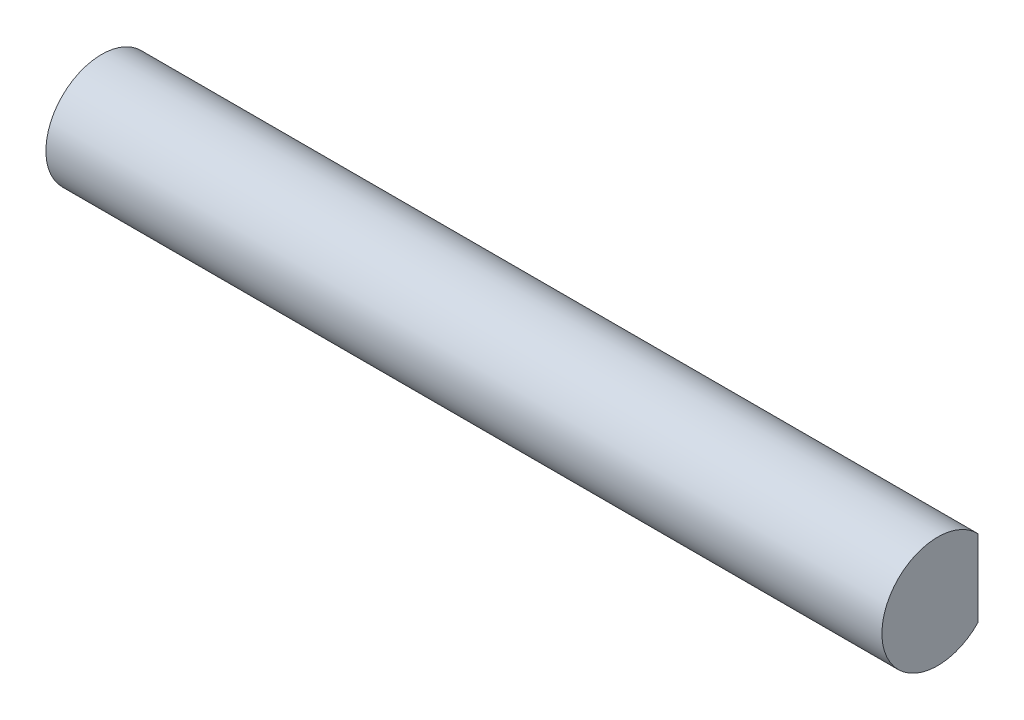
SolidWorks part; units mm, degrees
ref_plane "Front Plane" through (0, 0, 0) normal (0, 0, 1) x (1, 0, 0)
ref_plane "Top Plane" through (0, 0, 0) normal (0, 1, 0) x (1, 0, 0)
ref_plane "Right Plane" through (0, 0, 0) normal (1, 0, 0) x (0, 0, -1)
sketch "Sketch5" plane through (0, 0, 3.7) normal (1, 0, 0) x (0, 1, 0)
  line L0 (0, -16.5814) -> (0, 9.1814) construction
  line L5 (-7.5, -2.6947) -> (-6.4, -4.6) construction
  line L6 (7.5, -2.6947) -> (6.4, -4.6) construction
  line L7 (5.3668, 1) -> (7.5, -2.6947) construction
  line L8 (-5.3668, 1) -> (5.3668, 1) construction
  line L9 (-5.3668, 1) -> (-7.5, -2.6947) construction
  line L10 (7.7309, -2.6947) -> (6.5732, -4.7)
  line L11 (5.4823, 1.2) -> (7.7309, -2.6947)
  line L12 (-5.4823, 1.2) -> (5.4823, 1.2)
  line L13 (-5.4823, 1.2) -> (-7.7309, -2.6947)
  line L14 (-7.7309, -2.6947) -> (-6.5732, -4.7)
  line L15 (-6.5732, -4.7) -> (6.5732, -4.7)
  line L17 (0, -9.7207) -> (0, 9.7207) construction
  line L18 (-6.9, -10.9381) -> (6.9, -10.9381)
  line L19 (0, -10.9381) -> (0, -3.7) construction
  circle A0 centre (0, -3.7) radius 10 construction
  arc A1 (-6.9, -10.9381) -> (6.9, -10.9381) centre (0, -3.7) cw
  point P18 (0, -13.7)
sketch "Sketch8" plane through (0, 0, 3.7) normal (0, -1, 0) x (1, 0, 0)
  line L2 (0, -9.7207) -> (-145, -9.7207)
  line L3 (0, -9.9381) -> (-145, -9.9381)
  line L4 (0, -10.9381) -> (-150, -10.9381)
  point P0 (0, -9.7207)
  point P3 (0, -10.9381)
sketch "Sketch9" plane through (0, 0, 3.7) normal (1, 0, 0) x (0, 1, 0)
  line L0 (-6.9, -10.9381) -> (6.9, -10.9381) construction
  line L3 (-6.9, -10.9381) -> (6.9, -10.9381) construction
  line L4 (-6.4874, -9.9381) -> (6.4874, -9.9381)
  line L5 (-6.4017, -9.7381) -> (6.4017, -9.7381)
  arc A3 (6.9, -10.9381) -> (-6.9, -10.9381) centre (0, -3.7) ccw construction
  arc A4 (6.4874, -9.9381) -> (-6.4874, -9.9381) centre (0, -3.7) ccw
  arc A5 (6.4017, -9.7381) -> (-6.4017, -9.7381) centre (0, -3.7) ccw
sketch "Sketch1" plane through (0, 0, 0) normal (1, 0, 0) x (0, 0, -1)
  line L37 (7.2381, -6.9) -> (7.2381, 6.9) construction
  line L39 (7.2381, -6.9) -> (7.2381, 6.9)
  line L42 (1, 6.5732) -> (-1.0053, 7.7309)
  line L43 (1, -6.5732) -> (1, 6.5732)
  line L44 (-1.0053, -7.7309) -> (1, -6.5732)
  line L45 (-4.9, -5.4823) -> (-1.0053, -7.7309)
  line L46 (-4.9, 5.4823) -> (-4.9, -5.4823)
  line L47 (-1.0053, 7.7309) -> (-4.9, 5.4823)
  line L48 (1, 6.5732) -> (-1.0053, 7.7309)
  line L49 (1, -6.5732) -> (1, 6.5732)
  line L50 (-1.0053, -7.7309) -> (1, -6.5732)
  line L51 (-4.9, -5.4823) -> (-1.0053, -7.7309)
  line L52 (-4.9, 5.4823) -> (-4.9, -5.4823)
  line L53 (-1.0053, 7.7309) -> (-4.9, 5.4823)
  arc A5 (7.2381, 6.9) -> (7.2381, -6.9) centre (0, 0) ccw construction
  arc A6 (7.2381, 6.9) -> (7.2381, -6.9) centre (0, 0) ccw
  dimension "D2" = 0
extrude "Bar" add sketch "Sketch1" against normal up to vertex (150 mm away) up to point (-150, 0, -7.2381)
sketch "Sketch10" plane through (-150, 0, 0) normal (-1, 0, 0) x (0, 0, 1)
  line L0 (-6.2381, -6.4874) -> (-6.2381, 6.4874) construction
  line L1 (-6.2381, -6.4874) -> (-6.2381, 6.4874)
  arc A0 (-6.2381, -6.4874) -> (-6.2381, 6.4874) centre (0, 0) ccw construction
  arc A1 (-6.2381, -6.4874) -> (-6.2381, 6.4874) centre (0, 0) ccw
extrude "Cut-Extrude4" cut sketch "Sketch10" against normal up to vertex (5 mm away) up to point (-145, 0, -6.2381)
sketch "Sketch6" plane through (0, 0, -7.2381) normal (0, 0, -1) x (1, 0, 0)
  line L12 (0, 0) -> (-150, 0) construction
  line L13 (-0.8, 6.1) -> (-49.7333, 6.1)
  line L14 (-0.8, 6.1) -> (-0.8, -6.1)
  line L15 (-0.8, -6.1) -> (-49.7333, -6.1)
  line L24 (0, -6.9) -> (0, 6.9)
  line L25 (0, 6.9) -> (-150, 6.9)
  line L26 (-150, 6.9) -> (-150, -6.9)
  line L27 (-150, -6.9) -> (0, -6.9)
  line L28 (0, -6.9) -> (0, 6.9) construction
  line L29 (0, 6.9) -> (-150, 6.9) construction
  line L30 (-150, 6.9) -> (-150, -6.9) construction
  line L31 (-150, -6.9) -> (0, -6.9) construction
  line L32 (-49.7333, 6.1) -> (-49.7333, -6.1)
  line L33 (-50.5333, 6.1) -> (-50.5333, -6.1)
  line L34 (-50.5333, 6.1) -> (-99.4667, 6.1)
  line L35 (-99.4667, 6.1) -> (-99.4667, -6.1)
  line L36 (-50.5333, -6.1) -> (-99.4667, -6.1)
  line L37 (-100.2667, 6.1) -> (-100.2667, -6.1)
  line L38 (-100.2667, 6.1) -> (-149.2, 6.1)
  line L39 (-149.2, 6.1) -> (-149.2, -6.1)
  line L40 (-100.2667, -6.1) -> (-149.2, -6.1)
  dimension "D2" = 0.8
  dimension "D3" = 0.8
  dimension "D5" = 0.8
  dimension "D6" = 0.8
  dimension "D1" = 0
  dimension "D4" = 3
extrude "Cut-Extrude3" cut sketch "Sketch6" against normal up to next
sketch "Sketch11" plane through (0, 0, 0) normal (1, 0, 0) x (0, 0, -1)
  line L1 (7.2381, -6.9) -> (7.2381, 6.9)
  line L2 (7.2381, -6.9) -> (7.2381, 6.9)
  arc A1 (7.2381, 6.9) -> (7.2381, -6.9) centre (0, 0) ccw
  arc A2 (7.2381, 6.9) -> (7.2381, -6.9) centre (0, 0) ccw
  dimension "D1" = 0
extrude "Boss-Extrude2" add sketch "Sketch11" against normal blind 0.8
